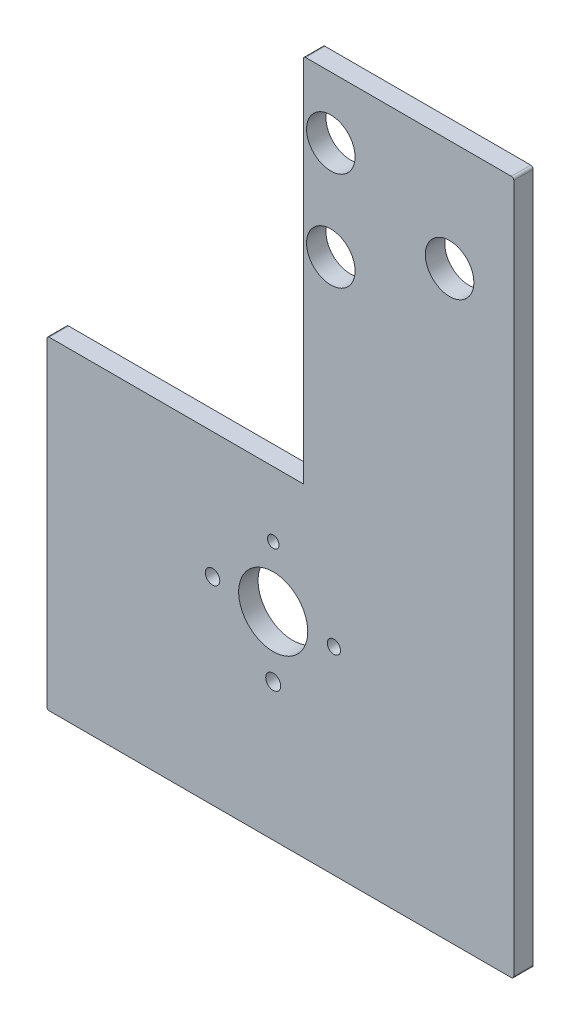
SolidWorks part; units mm, degrees
ref_plane "前视基准面" through (0, 0, 0) normal (0, 0, 1) x (1, 0, 0)
ref_plane "上视基准面" through (0, 0, 0) normal (0, 1, 0) x (1, 0, 0)
ref_plane "右视基准面" through (0, 0, 0) normal (1, 0, 0) x (0, 0, -1)
sketch "草图1" plane through (0, 0, 0) normal (0, 0, 1) x (1, 0, 0)
  line L0 (4236.3612, 3653.2795) -> (4045.9207, 3653.2795)
  line L1 (4237.3612, 3654.2795) -> (4237.3612, 3938.2882)
  line L2 (4044.9207, 3654.2795) -> (4044.9207, 3785.6264)
  line L3 (4045.9207, 3786.6264) -> (4150.6061, 3786.6264)
  line L4 (4150.6061, 3786.6264) -> (4150.6061, 3938.2882)
  line L5 (4151.6061, 3939.2882) -> (4236.3612, 3939.2882)
  arc A0 (4044.9207, 3654.2795) -> (4045.9207, 3653.2795) centre (4045.9207, 3654.2795) ccw
  arc A1 (4236.3612, 3653.2795) -> (4237.3612, 3654.2795) centre (4236.3612, 3654.2795) ccw
  arc A2 (4045.9207, 3786.6264) -> (4044.9207, 3785.6264) centre (4045.9207, 3785.6264) ccw
  circle A3 centre (4210.9113, 3893.6292) radius 10
  circle A4 centre (4161.9605, 3913.9702) radius 10
  circle A5 centre (4161.9605, 3873.2883) radius 10
  arc A6 (4151.6061, 3939.2882) -> (4150.6061, 3938.2882) centre (4151.6061, 3938.2882) ccw
  arc A7 (4237.3612, 3938.2882) -> (4236.3612, 3939.2882) centre (4236.3612, 3938.2882) ccw
  circle A8 centre (4138.2233, 3734.8187) radius 14.2377
extrude "凸台-拉伸1" add sketch "草图1" along normal blind 8
sketch "草图2" plane through (0, 0, 8) normal (0, 0, 1) x (1, 0, 0)
  circle A0 centre (4138.2233, 3734.8187) radius 25 construction
  circle A1 centre (4138.2233, 3759.8187) radius 2.3888
  circle A2 centre (4163.2233, 3734.8187) radius 2.7197
  circle A3 centre (4138.2233, 3709.8187) radius 3.0863
  circle A4 centre (4113.2233, 3734.8187) radius 2.9783
  dimension "D1" = 50
extrude "切除-拉伸1" cut sketch "草图2" against normal through all
